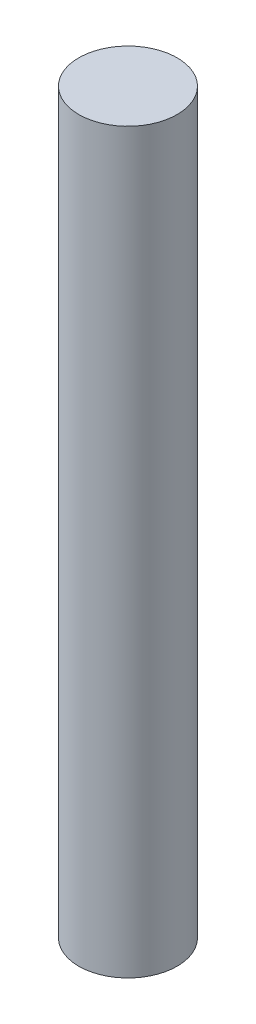
SolidWorks part; units mm, degrees
ref_plane "Front Plane" through (0, 0, 0) normal (0, 0, 1) x (1, 0, 0)
ref_plane "Top Plane" through (0, 0, 0) normal (0, 1, 0) x (1, 0, 0)
ref_plane "Right Plane" through (0, 0, 0) normal (1, 0, 0) x (0, 0, -1)
sketch "Sketch1" plane through (0, 0, 0) normal (0, 1, 0) x (1, 0, 0)
  circle A0 centre (0, 0) radius 20
extrude "Boss-Extrude1" add sketch "Sketch1" along normal blind 300
